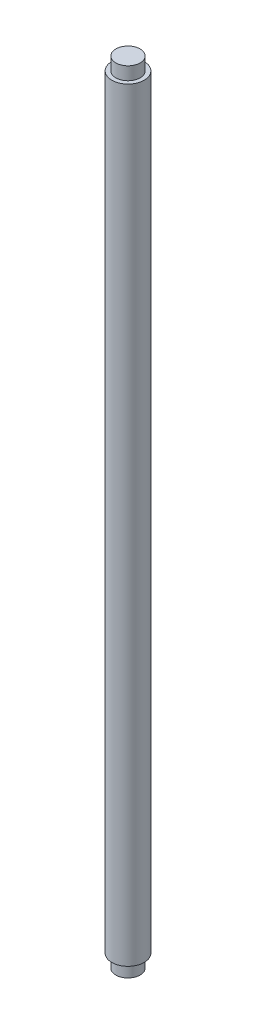
SolidWorks part; units mm, degrees
ref_plane "Alzado" through (0, 0, 0) normal (0, 0, 1) x (1, 0, 0)
ref_plane "Planta" through (0, 0, 0) normal (0, 1, 0) x (1, 0, 0)
ref_plane "Vista lateral" through (0, 0, 0) normal (1, 0, 0) x (0, 0, -1)
sketch "Croquis1" plane through (0, 0, 0) normal (0, 1, 0) x (1, 0, 0)
  circle A0 centre (0, 0) radius 2.5
  dimension "D1" = 5
extrude "Saliente-Extruir1" add sketch "Croquis1" along normal blind 118
sketch "Croquis2" plane through (0, 118, 0) normal (0, 1, 0) x (1, 0, 0)
  circle A0 centre (0, 0) radius 1.875
  dimension "D1" = 3.75
extrude "Saliente-Extruir2" add sketch "Croquis2" along normal blind 2
sketch "Croquis3" plane through (0, 0, 0) normal (0, -1, 0) x (1, 0, 0)
  circle A0 centre (0, 0) radius 1.875
  dimension "D1" = 3.75
extrude "Saliente-Extruir3" add sketch "Croquis3" along normal blind 2
